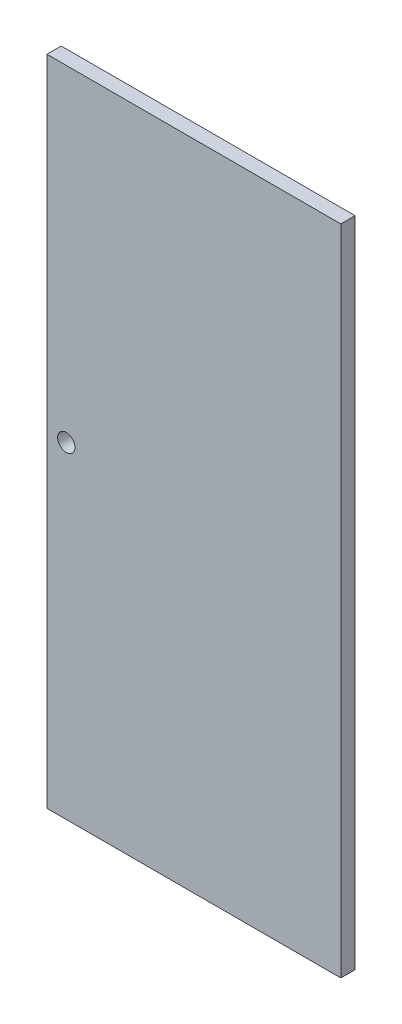
SolidWorks part; units mm, degrees
material "1023 Carbon Steel Sheet (SS)"
ref_plane "Front Plane" through (0, 0, 0) normal (0, 0, 1) x (1, 0, 0)
ref_plane "Top Plane" through (0, 0, 0) normal (0, 1, 0) x (1, 0, 0)
ref_plane "Right Plane" through (0, 0, 0) normal (1, 0, 0) x (0, 0, -1)
sketch "Sketch1" plane through (0, 0, 0) normal (0, 0, 1) x (1, 0, 0)
  line L1 (658.971, 2.3929) -> (1573.371, 2.3929)
  line L2 (658.971, 2.3929) -> (658.971, 2034.3929)
  line L3 (658.971, 2034.3929) -> (1573.371, 2034.3929)
  line L4 (1573.371, 2.3929) -> (1573.371, 2034.3929)
  dimension "D1" = 2032
  dimension "D2" = 914.4
extrude "Boss-Extrude1" add sketch "Sketch1" along normal blind 44.45
sketch "Sketch2" plane through (0, 0, 44.45) normal (0, 0, 1) x (1, 0, 0)
  line L0 (658.971, 2.3929) -> (1573.371, 2.3929) construction
  line L1 (658.971, 2034.3929) -> (658.971, 2.3929) construction
  circle A0 centre (719.296, 1018.3929) radius 26.9875
  dimension "D3" = 53.975
  dimension "D1" = 1016
  dimension "D2" = 60.325
extrude "Cut-Extrude1" cut sketch "Sketch2" against normal blind 44.45
